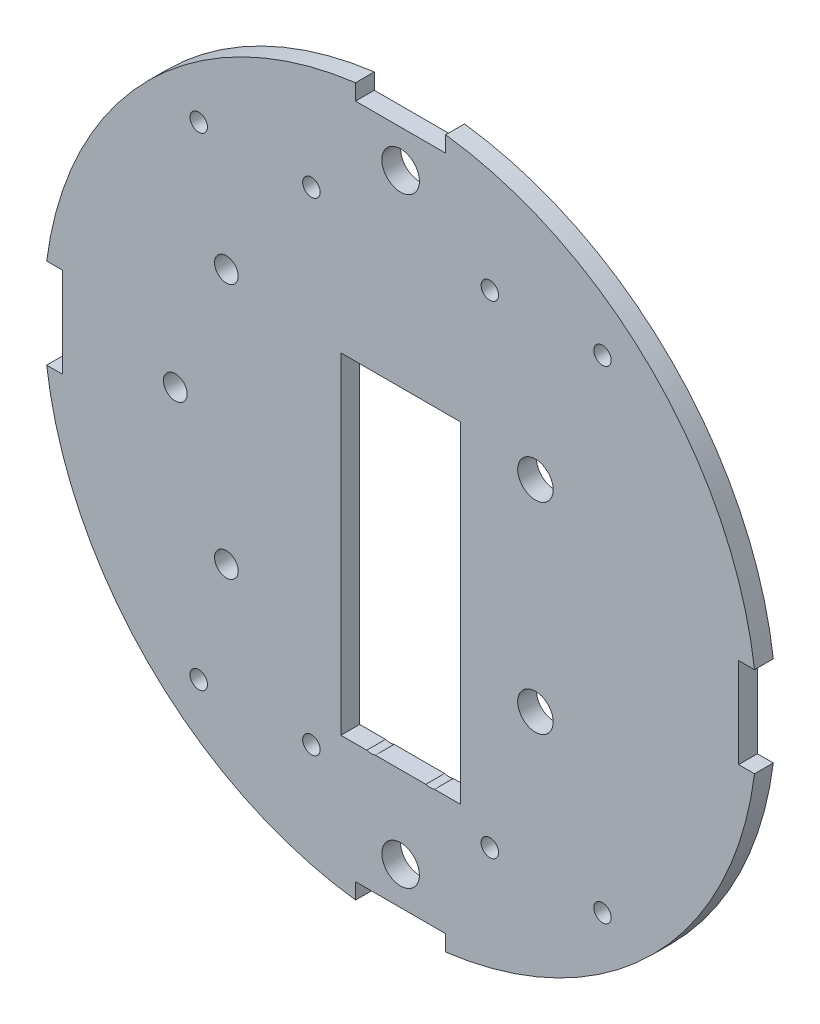
SolidWorks part; units mm, degrees
material "A-Glass Fiber"
ref_plane "Front Plane" through (0, 0, 0) normal (0, 0, 1) x (1, 0, 0)
ref_plane "Top Plane" through (0, 0, 0) normal (0, 1, 0) x (1, 0, 0)
ref_plane "Right Plane" through (0, 0, 0) normal (1, 0, 0) x (0, 0, -1)
sketch "Sketch1" plane through (0, 0, 0) normal (0, 0, 1) x (1, 0, 0)
  circle A0 centre (0, 0) radius 60.325
  dimension "D1" = 120.65
extrude "Boss-Extrude1" add sketch "Sketch1" along normal blind 3.175
sketch "Sketch2" plane through (0, 0, 3.175) normal (0, 0, 1) x (1, 0, 0)
  line L0 (0, 0) -> (0, 60.325) construction
  line L2 (-7.62, 57.15) -> (7.62, 57.15)
  line L3 (-7.62, 57.15) -> (-7.62, 63.5)
  line L4 (-7.62, 63.5) -> (7.62, 63.5)
  line L5 (7.62, 57.15) -> (7.62, 63.5)
  line L6 (-7.62, 57.15) -> (7.62, 63.5) construction
  line L7 (-7.62, 63.5) -> (7.62, 57.15) construction
  circle A0 centre (0, 0) radius 60.325 construction
  circle A1 centre (0, 50.8) radius 3.175
  dimension "D3" = 50.8
  dimension "D1" = 15.24
  dimension "D2" = 6.35
extrude "Cut-Extrude1" cut sketch "Sketch2" against normal blind 3.175 contours L5 L4 L3 L2 | A1
pattern_circular "CirPattern1" count 4 every 90 about axis through (0, 0, 0) along (0, 0, 1) of "Cut-Extrude1"
sketch "Sketch3" plane through (0, 0, 3.175) normal (0, 0, 1) x (1, 0, 0)
  line L0 (-29.464, 21.59) -> (-29.464, -21.59) construction
  line L1 (-38.1, 0) -> (-29.464, 0) construction
  line L2 (-10.1, 19.05) -> (-10.1, -35.95)
  line L3 (10.1, 19.05) -> (-10.1, 19.05)
  line L4 (22.8, -17.0548) -> (22.8, 16.9452) construction
  line L6 (10.1, -35.95) -> (10.1, 2.35)
  line L7 (-9.1, -36.95) -> (9.1, -36.95)
  line L8 (-9.1, -36.95) -> (-10.1, -36.95)
  line L9 (-10.1, -36.95) -> (-10.1, -35.95)
  line L10 (9.1, -36.95) -> (10.1, -36.95)
  line L11 (10.1, -36.95) -> (10.1, -35.95)
  line L12 (10.1, 2.35) -> (10.1, 19.05)
  circle A0 centre (-38.1, 0) radius 2
  circle A1 centre (-29.464, 21.59) radius 2
  circle A2 centre (-29.464, -21.59) radius 2
  circle A3 centre (-50.8, 0) radius 3.175 construction
  circle A4 centre (22.8, 16.9452) radius 3
  circle A5 centre (22.8, -17.0548) radius 3
  point P22 (22.8, -0.0548)
  dimension "D1" = 55
  dimension "D3" = 4
  dimension "D6" = 12.7
  dimension "D2" = 19.05
  dimension "D4" = 21.59
  dimension "D5" = 8.636
  dimension "D7" = 34
  dimension "D8" = 12.7
extrude "Cut-Extrude2" cut sketch "Sketch3" against normal blind 3.175
sketch "Sketch4" plane through (0, 0, 0) normal (0, 0, -1) x (-1, 0, 0)
  circle A0 centre (5, -34.65) radius 2.413
  circle A1 centre (-5, -34.65) radius 2.413
  circle A2 centre (-5, 13.35) radius 2.413
  circle A3 centre (5, 13.35) radius 2.413
extrude "Cut-Extrude3" cut sketch "Sketch4" against normal blind 3.175
sketch "Sketch5" plane through (0, 0, 0) normal (0, 0, -1) x (-1, 0, 0)
  circle A0 centre (-50.8, 0) radius 3.175
  circle A1 centre (50.8, 0) radius 3.175
extrude "Boss-Extrude2" add sketch "Sketch5" against normal blind 3.175
sketch "Sketch6" plane through (0, 0, 3.175) normal (0, 0, 1) x (1, 0, 0)
  line L0 (0, 57.15) -> (0, -57.15) construction
  line L1 (-7.62, 57.15) -> (7.62, 57.15) construction
  line L2 (7.62, -57.15) -> (-7.62, -57.15) construction
  circle A4 centre (15.0843, 40.8119) radius 1.4732
  circle A5 centre (34.1343, 40.8119) radius 1.4732
  circle A6 centre (34.1343, -40.8119) radius 1.4732
  circle A7 centre (15.0843, -40.8119) radius 1.4732
  circle A8 centre (-15.0843, -40.8119) radius 1.4732
  circle A9 centre (-34.1343, -40.8119) radius 1.4732
  circle A10 centre (-34.1343, 40.8119) radius 1.4732
  circle A11 centre (-15.0843, 40.8119) radius 1.4732
extrude "Cut-Extrude4" cut sketch "Sketch6" against normal through all
